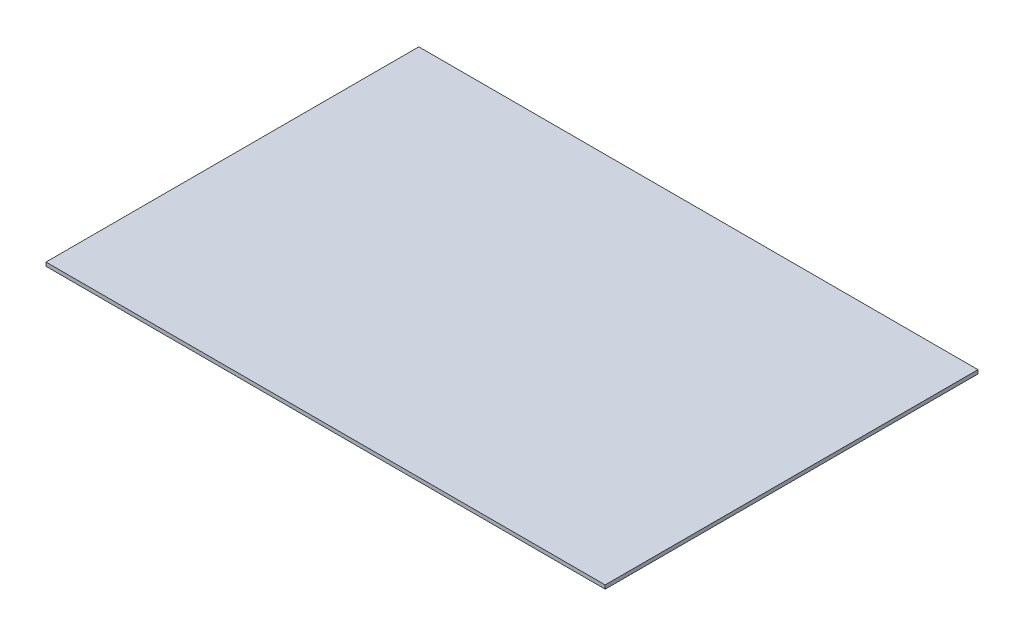
SolidWorks part; units mm, degrees
ref_plane "Front Plane" through (0, 0, 0) normal (0, 0, 1) x (1, 0, 0)
ref_plane "Top Plane" through (0, 0, 0) normal (0, 1, 0) x (1, 0, 0)
ref_plane "Right Plane" through (0, 0, 0) normal (1, 0, 0) x (0, 0, -1)
sketch "Sketch1" plane through (0, 0, 0) normal (0, 1, 0) x (1, 0, 0)
  line L1 (-750, 500) -> (750, 500)
  line L2 (-750, 500) -> (-750, -500)
  line L3 (-750, -500) -> (750, -500)
  line L4 (750, 500) -> (750, -500)
  line L5 (-750, 500) -> (750, -500) construction
  line L6 (-750, -500) -> (750, 500) construction
  point P0 (0, 0)
  dimension "D1" = 1500
  dimension "D2" = 1000
extrude "Boss-Extrude1" add sketch "Sketch1" along normal blind 10
